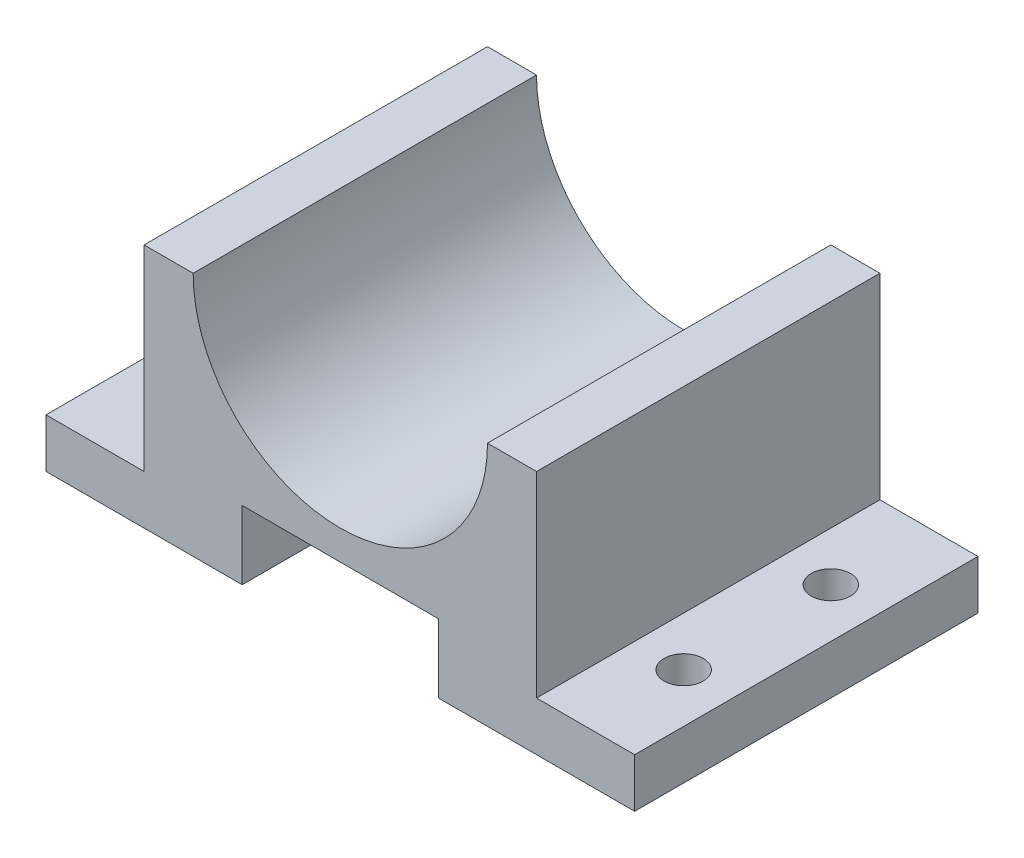
SolidWorks part; units mm, degrees
ref_plane "Ön Düzlem" through (0, 0, 0) normal (0, 0, 1) x (1, 0, 0)
ref_plane "Üst Düzlem" through (0, 0, 0) normal (0, 1, 0) x (1, 0, 0)
ref_plane "Sağ Düzlem" through (0, 0, 0) normal (1, 0, 0) x (0, 0, -1)
sketch "Çizim1" plane through (0, 0, 0) normal (0, 0, 1) x (1, 0, 0)
  line L1 (0, 0) -> (60, 0)
  line L2 (0, 0) -> (0, 25)
  line L3 (0, 25) -> (60, 25)
  line L4 (60, 0) -> (60, 25)
  dimension "D1" = 60
  dimension "D2" = 25
extrude "Yükseklik-Ekstrüzyon1" add sketch "Çizim1" along normal blind 35
sketch "Çizim2" plane through (0, 0, 35) normal (0, 0, 1) x (1, 0, 0)
  line L0 (30, 25) -> (30, 0) construction
  line L1 (0, 25) -> (10, 25)
  line L2 (0, 25) -> (0, 5)
  line L3 (0, 5) -> (10, 5)
  line L4 (10, 25) -> (10, 5)
  line L5 (60, 25) -> (0, 25) construction
  line L6 (0, 0) -> (60, 0) construction
  line L7 (50, 25) -> (50, 5)
  line L8 (60, 5) -> (50, 5)
  line L9 (60, 25) -> (60, 5)
  line L10 (60, 25) -> (50, 25)
  line L11 (0, 25) -> (0, 0) construction
  line L12 (20, 0) -> (40, 0)
  line L13 (20, 0) -> (20, 7)
  line L14 (20, 7) -> (40, 7)
  line L15 (40, 0) -> (40, 7)
  line L16 (10, 25) -> (50, 25)
  line L17 (15, 25) -> (45, 25)
  line L18 (45, 25) -> (44.819, 25.1888)
  arc A0 (15, 25) -> (45, 25) centre (30, 25) ccw
  point P10 (30, 25)
  point P13 (30, 0)
  line M8 (0, 25) -> (0, 0)
  line M9 (0, 0) -> (60, 0)
  line M10 (60, 0) -> (60, 25)
  line M11 (60, 25) -> (0, 25)
  dimension "D6" = 30
  dimension "D1" = 10
  dimension "D2" = 20
  dimension "D3" = 20
  dimension "D4" = 20
  dimension "D5" = 7
extrude "Kes-Ekstrüzyon2" cut sketch "Çizim2" against normal through all contours L4 L3 M11 M8 | L0 L17 A0 | L16 L0 A0 | L8 L7 M10 M11 | L14 L0 L12 L15 | L0 L14 L13 M9
sketch "Çizim3" plane through (0, 5, 0) normal (0, 1, 0) x (1, 0, 0)
  line L0 (0, -17.5) -> (10, -17.5) construction
  line L4 (0, 0) -> (0, -35) construction
  line L5 (10, 0) -> (10, -35) construction
  line L6 (5, 0) -> (5, -35) construction
  line L7 (0, 0) -> (10, 0) construction
  line L8 (0, -35) -> (10, -35) construction
  line L9 (30, 0) -> (30, -35) construction
  line L10 (45, 0) -> (15, 0) construction
  line L11 (15, -35) -> (45, -35) construction
  line L12 (55, 0) -> (55, -35) construction
  line L13 (60, -17.5) -> (50, -17.5) construction
  circle A0 centre (5, -25) radius 2
  circle A1 centre (5, -10) radius 2
  circle A2 centre (55, -10) radius 2
  circle A3 centre (55, -25) radius 2
  dimension "D1" = 4
  dimension "D2" = 10
extrude "Kes-Ekstrüzyon3" cut sketch "Çizim3" against normal through all
